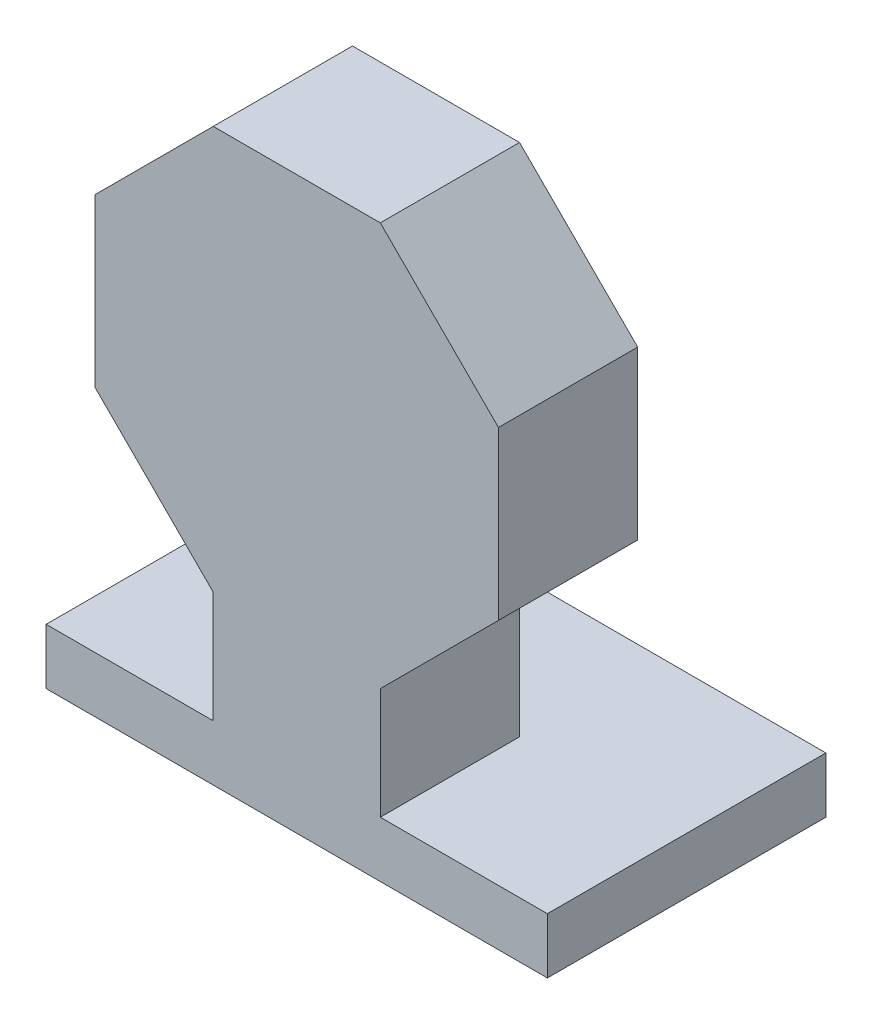
SolidWorks part; units mm, degrees
ref_plane "Front" through (0, 0, 0) normal (0, 0, 1) x (1, 0, 0)
ref_plane "Top" through (0, 0, 0) normal (0, 1, 0) x (1, 0, 0)
ref_plane "Right" through (0, 0, 0) normal (1, 0, 0) x (0, 0, -1)
sketch "Sketch2" plane through (0, 0, 0) normal (0, 0, 1) x (1, 0, 0)
  line L0 (15, -36.2132) -> (15, -56.2132)
  line L1 (36.2132, 15) -> (15, 36.2132)
  line L2 (15, 36.2132) -> (-15, 36.2132)
  line L3 (-15, 36.2132) -> (-36.2132, 15)
  line L4 (-36.2132, 15) -> (-36.2132, -15)
  line L5 (-36.2132, -15) -> (-15, -36.2132)
  line L7 (15, -36.2132) -> (36.2132, -15)
  line L8 (36.2132, -15) -> (36.2132, 15)
  line L9 (15, -56.2132) -> (-15, -56.2132)
  line L10 (-15, -56.2132) -> (-15, -36.2132)
  line L12 (-15, -36.2132) -> (0, -36.2132) [skipped]
  arc A0 (25.6066, -25.6066) -> (-25.6066, -25.6066) centre (0, 0) ccw construction
  dimension "D1" = 30
  dimension "D2" = 20
extrude "Extrude1" add sketch "Sketch2" along normal blind 25
sketch "Sketch3" plane through (0, -56.2132, 0) normal (0, -1, 0) x (1, 0, 0)
  line L2 (-45, 25) -> (-45, -25)
  line L3 (45, 25) -> (45, -25)
  line L4 (45, 25) -> (-45, 25)
  line L5 (-45, -25) -> (45, -25)
extrude "Extrude2" add sketch "Sketch3" along normal blind 10
